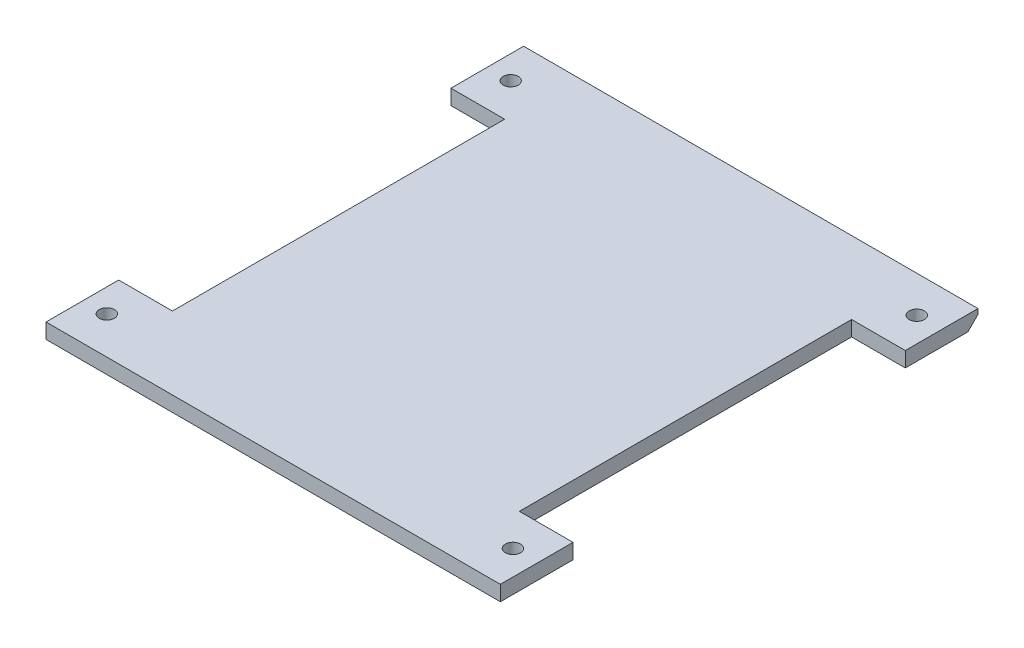
SolidWorks part; units mm, degrees
ref_plane "Front Plane" through (0, 0, 0) normal (0, 0, 1) x (1, 0, 0)
ref_plane "Top Plane" through (0, 0, 0) normal (0, 1, 0) x (1, 0, 0)
ref_plane "Right Plane" through (0, 0, 0) normal (1, 0, 0) x (0, 0, -1)
sketch "Sketch2" plane through (0, 0, 0) normal (0, 1, 0) x (1, 0, 0)
  line L0 (45, -47.305) -> (45, 47.305)
  line L1 (45, 47.305) -> (-45, 47.305)
  line L2 (45, -47.305) -> (-45, -47.305)
  line L3 (-45, -47.305) -> (-45, 47.305)
  circle A0 centre (40.0829, -39.905) radius 1.5
  circle A1 centre (-40.3571, -39.905) radius 1.5
  circle A2 centre (40.0829, 40.095) radius 1.5
  circle A3 centre (-40.3571, 40.095) radius 1.5
extrude "Boss-Extrude1" add sketch "Sketch2" along normal blind 3
sketch "Sketch3" plane through (0, 0, 0) normal (0, -1, 0) x (-1, 0, 0)
  line L0 (45, 47.305) -> (45, 32.905) construction
  line L1 (45, 47.305) -> (45, -47.305) construction
  line L2 (45, 32.905) -> (34.36, 32.905)
  line L3 (45, 0) -> (-6.6411, 0) construction
  line L4 (45, 32.905) -> (45, -32.905)
  line L5 (34.36, 32.905) -> (34.36, -32.905)
  line L6 (45, -32.905) -> (34.36, -32.905)
  line L7 (0, 47.305) -> (0, -47.305) construction
  line L8 (-45, 47.305) -> (45, 47.305) construction
  line L9 (45, -47.305) -> (-45, -47.305) construction
  line L10 (-45, -32.905) -> (-34.36, -32.905)
  line L11 (-34.36, 32.905) -> (-34.36, -32.905)
  line L12 (-45, 32.905) -> (-45, -32.905)
  line L13 (-45, 32.905) -> (-34.36, 32.905)
  point P15 (34.36, 0)
extrude "Cut-Extrude1" cut sketch "Sketch3" against normal blind 10
chamfer "Chamfer1" distance 2 angle 45 1 edges at (0, 0, -47.305)
